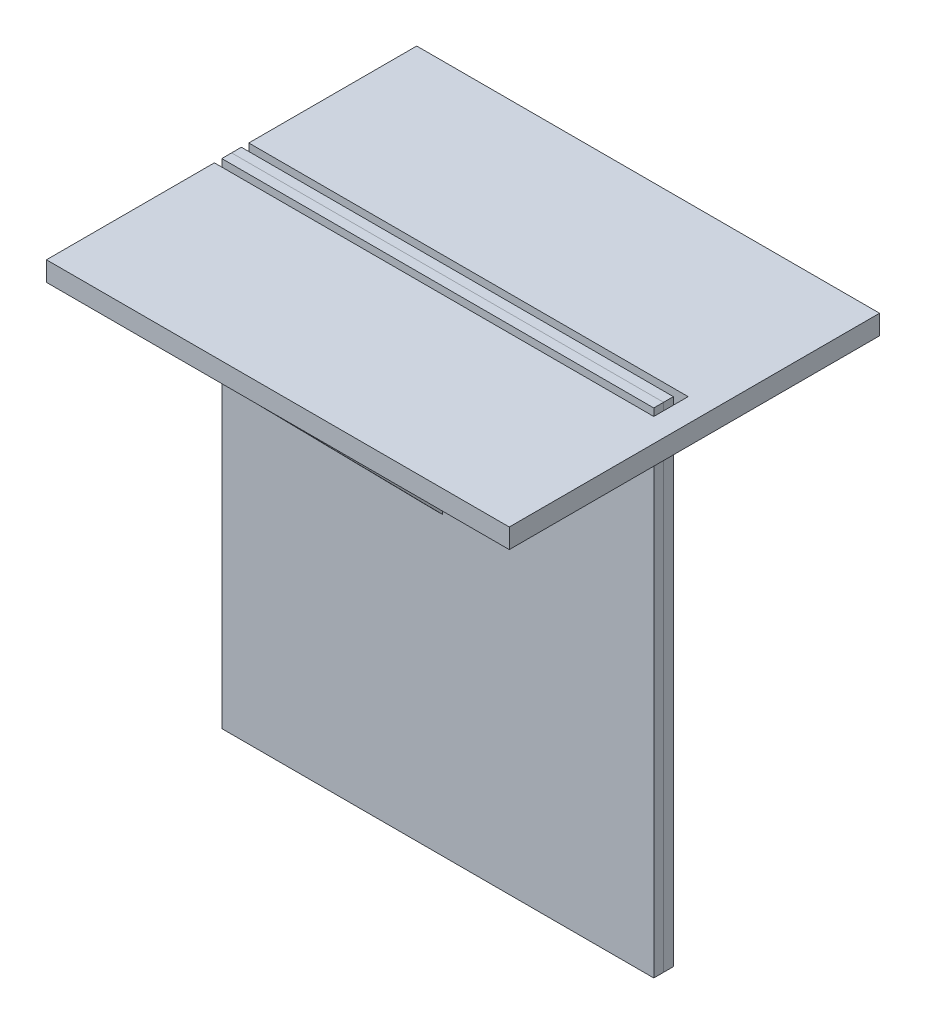
SolidWorks part; units mm, degrees
material "Balsa"
ref_plane "Front Plane" through (0, 0, 0) normal (0, 0, 1) x (1, 0, 0)
ref_plane "Top Plane" through (0, 0, 0) normal (0, 1, 0) x (1, 0, 0)
ref_plane "Right Plane" through (0, 0, 0) normal (1, 0, 0) x (0, 0, -1)
sketch "Sketch1" plane through (0, 0, 0) normal (0, 0, 1) x (1, 0, 0)
  line L0 (788.9482, 49) -> (-611.0518, 49) construction
  line L1 (35, -31) -> (-35, -31)
  line L2 (35, -31) -> (35, 49)
  line L3 (35, 49) -> (-35, 49)
  line L4 (-35, -31) -> (-35, 49)
  point P6 (0, -31)
  dimension "D1" = 80
  dimension "D2" = 70
extrude "Boss-Extrude1" add sketch "Sketch1" along normal blind 1.5875
sketch "Sketch2" plane through (0, 0, 0) normal (0, 0, -1) x (-1, 0, 0)
  line L4 (-35, 49) -> (-35, -31)
  line L5 (-35, -31) -> (35, -31)
  line L6 (35, -31) -> (35, 49)
  line L7 (35, 49) -> (-35, 49)
  line L8 (-35, 49) -> (-35, -31)
  line L9 (-35, -31) -> (35, -31)
  line L10 (35, -31) -> (35, 49)
  line L11 (35, 49) -> (-35, 49)
  circle A0 centre (0, 0) radius 18.25
  circle A1 centre (0, 0) radius 18 construction
  dimension "D2" = 0.25
  dimension "D1" = 0
extrude "Boss-Extrude2" add sketch "Sketch2" along normal blind 1.5875 separate body
sketch "Sketch3" plane through (0, 49, 0) normal (0, -1, 0) x (1, 0, 0)
  line L0 (-35, 1.5875) -> (-35, 0) construction
  line L1 (-35, 30) -> (40, 30)
  line L2 (-35, 30) -> (-35, 2.7875)
  line L3 (-35, -30) -> (40, -30)
  line L4 (40, 30) -> (40, -30)
  line L6 (35, 0) -> (-35, 0) construction
  line L15 (-35, -2.7875) -> (-35, -30)
  line L23 (36.2, -2.7875) -> (-35, -2.7875)
  line L24 (36.2, 0) -> (36.2, -2.7875)
  line L25 (36.2, 2.7875) -> (36.2, 0)
  line L26 (-35, 2.7875) -> (36.2, 2.7875)
  line L27 (36.2, -2.7875) -> (-35, -2.7875)
  line L28 (36.2, 0) -> (36.2, -2.7875)
  line L29 (36.2, 2.7875) -> (36.2, 0)
  line L30 (-35, 2.7875) -> (36.2, 2.7875)
  point P8 (40, 0)
  point P11 (0, 0)
  dimension "D1" = 60
  dimension "D2" = 75
  dimension "D3" = 1.2
extrude "Boss-Extrude3" add sketch "Sketch3" along normal blind 3.175 separate body
ref_plane "Plane1" through (0, 0, 0) normal (-1, 0, 0) x (0, 0, 1)
sketch "Sketch5" plane through (0, 0, 0) normal (-1, 0, 0) x (0, 0, 1)
  line L0 (30, 45.825) -> (1.5875, 16.9342)
  line L1 (1.5875, 49) -> (1.5875, -31) construction
  line L2 (30, 45.825) -> (2.7875, 45.825) construction
  line L3 (1.5875, 16.9342) -> (1.5875, 45.825)
  line L4 (-30, 45.825) -> (30, 45.825) construction
  line L5 (1.5875, 45.825) -> (30, 45.825)
  dimension "D1" = 45.478
extrude "Boss-Extrude4" add sketch "Sketch5" along normal mid plane 1.5875 separate body
